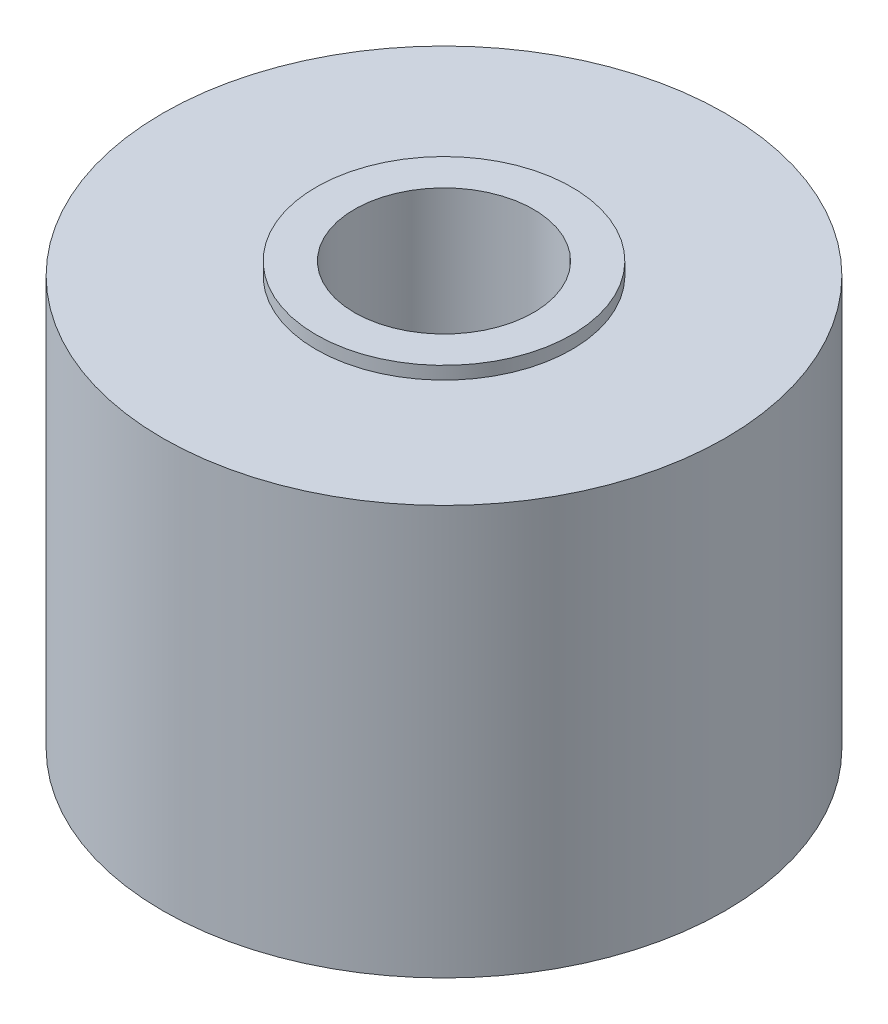
SolidWorks part; units mm, degrees
ref_plane "Front Plane" through (0, 0, 0) normal (0, 0, 1) x (1, 0, 0)
ref_plane "Top Plane" through (0, 0, 0) normal (0, 1, 0) x (1, 0, 0)
ref_plane "Right Plane" through (0, 0, 0) normal (1, 0, 0) x (0, 0, -1)
sketch "Sketch1" plane through (0, 0, 0) normal (0, 1, 0) x (1, 0, 0)
  circle A0 centre (0, 0) radius 11
extrude "Boss-Extrude1" add sketch "Sketch1" along normal blind 16
sketch "Sketch2" plane through (0, 16, 0) normal (0, 1, 0) x (1, 0, 0)
  circle A0 centre (0, 0) radius 5
  dimension "D1" = 10
extrude "Boss-Extrude2" add sketch "Sketch2" along normal blind 0.5
sketch "Sketch3" plane through (0, 0, 0) normal (0, -1, 0) x (1, 0, 0)
  circle A0 centre (0, 0) radius 9
extrude "Boss-Extrude3" add sketch "Sketch3" along normal blind 0.5
sketch "Sketch4" plane through (0, 16.5, 0) normal (0, 1, 0) x (1, 0, 0)
  circle A0 centre (0, 0) radius 3.5
extrude "Cut-Extrude1" cut sketch "Sketch4" against normal through all
